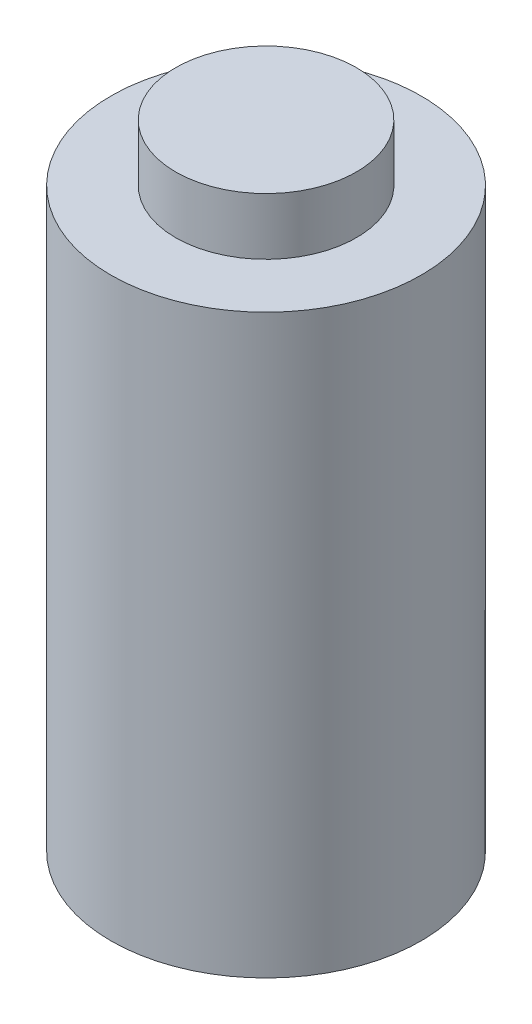
SolidWorks part; units mm, degrees
ref_plane "Front Plane" through (0, 0, 0) normal (0, 0, 1) x (1, 0, 0)
ref_plane "Top Plane" through (0, 0, 0) normal (0, 1, 0) x (1, 0, 0)
ref_plane "Right Plane" through (0, 0, 0) normal (1, 0, 0) x (0, 0, -1)
sketch "Sketch1" plane through (0, 0, 0) normal (0, 1, 0) x (1, 0, 0)
  circle A0 centre (0, 0) radius 16.8
  circle A1 centre (0, 0) radius 21.8
  dimension "D1" = 33.6
  dimension "5" = 5
extrude "Boss-Extrude1" add sketch "Sketch1" along normal blind 80
sketch "Sketch3" plane through (0, 80, 0) normal (0, 1, 0) x (1, 0, 0)
  circle A0 centre (0, 0) radius 21.8
extrude "Boss-Extrude2" add sketch "Sketch3" along normal blind 1
sketch "Sketch4" plane through (0, 81, 0) normal (0, 1, 0) x (1, 0, 0)
  circle A0 centre (0, 0) radius 12.7
  dimension "D1" = 25.4
extrude "Boss-Extrude3" add sketch "Sketch4" along normal blind 8
sketch "Sketch5" plane through (0, 89, 0) normal (0, 1, 0) x (1, 0, 0)
  line L0 (0, 0) -> (0, 12.7) construction
  line L1 (-12.7, 0) -> (12.7, 0) construction
  circle A0 centre (0, 0) radius 12.7 construction
  circle A1 centre (0, 0) radius 12.7 construction
